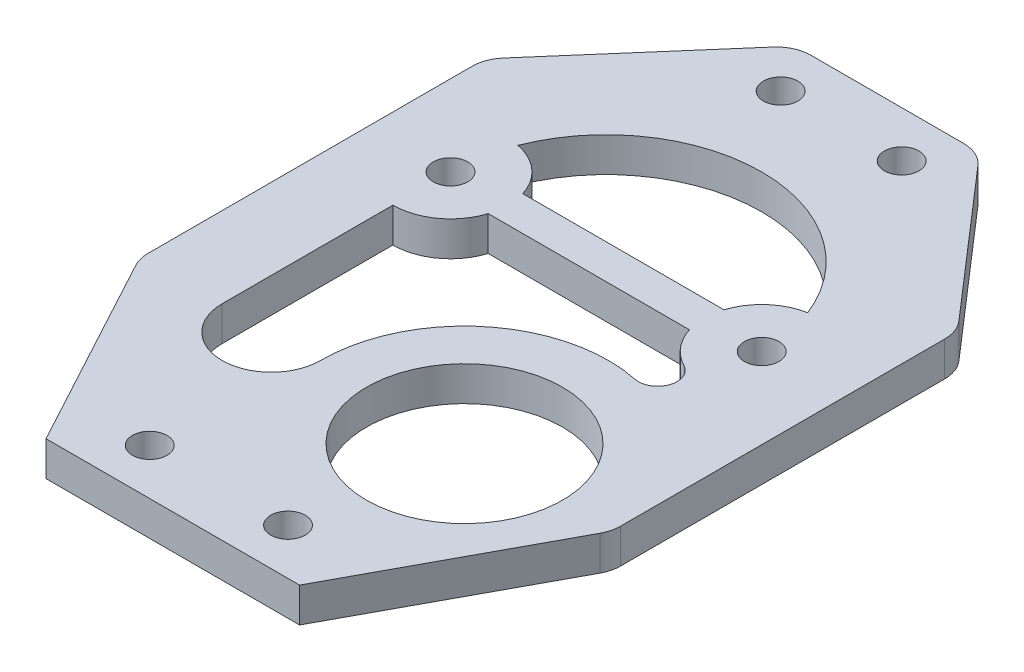
SolidWorks part; units mm, degrees
material "1060 Alloy"
ref_plane "Alzado" through (0, 0, 0) normal (0, 0, 1) x (1, 0, 0)
ref_plane "Planta" through (0, 0, 0) normal (0, 1, 0) x (1, 0, 0)
ref_plane "Vista lateral" through (0, 0, 0) normal (1, 0, 0) x (0, 0, -1)
sketch "Croquis1" plane through (0, 0, 0) normal (0, 1, 0) x (1, 0, 0)
  line L0 (0, 0) -> (0, 62) construction
  line L1 (-11, 0) -> (11, 0)
  line L2 (11, 0) -> (20.5, 17.5997)
  line L3 (20.5, 17.5997) -> (20.5, 47.5997)
  line L4 (20.5, 47.5997) -> (8, 62)
  line L5 (8, 62) -> (-8, 62)
  line L6 (-11, 0) -> (-20.5, 17.5997)
  line L7 (-20.5, 17.5997) -> (-20.5, 47.5997)
  line L8 (-20.5, 47.5997) -> (-8, 62)
  line L9 (7.5302, 17.7823) -> (10.3802, 23.0622) construction
  line L10 (10.3802, 23.0622) -> (20.5, 17.5997) construction
  line L11 (-5.25, 57.9943) -> (5.25, 57.9943) construction
  line L12 (-13.5, 37.5997) -> (13.5, 37.5997) construction
  line L13 (-8.7303, 39.0997) -> (8.7303, 39.0997)
  line L14 (-13.5, 32.5997) -> (-13.5, 17.7823)
  line L15 (-8.7303, 36.0997) -> (8.7303, 36.0997)
  line L16 (0, 39.0997) -> (0, 36.0997) construction
  line L17 (-6, 4) -> (6, 4) construction
  circle A0 centre (7.5302, 17.7823) radius 8.5
  circle A1 centre (-5.25, 57.9943) radius 1.5
  circle A2 centre (-13.5, 37.5997) radius 1.5
  circle A3 centre (13.5, 37.5997) radius 1.5
  circle A4 centre (5.25, 57.9943) radius 1.5
  arc A5 (8.7303, 39.0997) -> (12.5741, 42.5132) centre (13.5, 37.5997) cw
  arc A6 (-8.7303, 39.0997) -> (-12.5741, 42.5132) centre (-13.5, 37.5997) ccw
  arc A7 (12.5741, 42.5132) -> (-12.5741, 42.5132) centre (0, 37.5997) ccw
  arc A8 (10.0668, 30.0222) -> (-4.9698, 17.7823) centre (7.5302, 17.7823) ccw
  arc A9 (-13.5, 17.7823) -> (-4.9698, 17.7823) centre (-9.2349, 17.7823) ccw
  arc A10 (-13.5, 32.5997) -> (-8.7303, 36.0997) centre (-13.5, 37.5997) ccw
  arc A11 (8.7303, 36.0997) -> (11.188, 33.1664) centre (13.5, 37.5997) ccw
  arc A12 (11.188, 33.1664) -> (10.0668, 30.0222) centre (10.4088, 31.6722) cw
  circle A13 centre (-6, 4) radius 1.5
  circle A14 centre (6, 4) radius 1.5
  point P23 (0, 57.9943)
  point P24 (0, 37.5997)
  point P42 (0, 4)
  dimension "D7" = 17
  dimension "D8" = 11.5
  dimension "D9" = 6
  dimension "D10" = 3
  dimension "D15" = 4
  dimension "D17" = 5
  dimension "D18" = 13.5
  dimension "D20" = 12
  dimension "D1" = 62
  dimension "D2" = 41
  dimension "D3" = 22
  dimension "D4" = 16
  dimension "D5" = 30
  dimension "D6" = 20
  dimension "D11" = 10.5
  dimension "D12" = 27
  dimension "D13" = 22
  dimension "D14" = 10
  dimension "D16" = 3
  dimension "D19" = 45
  dimension "D21" = 4
extrude "Saliente-Extruir1" add sketch "Croquis1" along normal mid plane 3 contours L8 L5 L4 L3 L2 L1 L6 L7
fillet "Redondeo1" radius 3 6 edges at (-8, 0, -62) (8, 0, -62) (20.5, 0, -47.5997) (20.5, 0, -17.5997) (-20.5, 0, -17.5997) (-20.5, 0, -47.5997)
